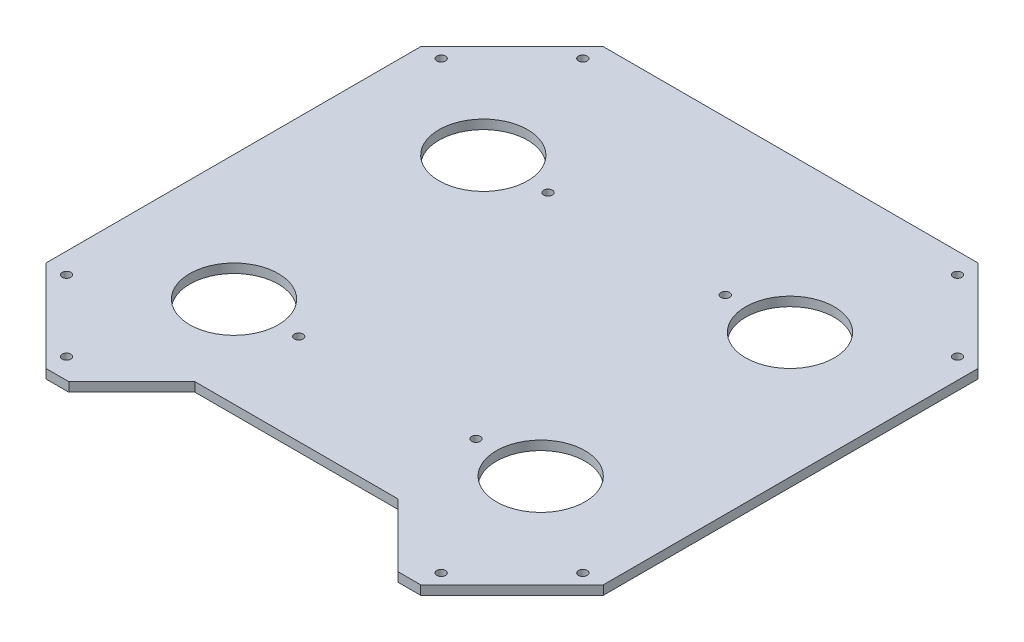
SolidWorks part; units mm, degrees
ref_plane "Front Plane" through (0, 0, 0) normal (0, 0, 1) x (1, 0, 0)
ref_plane "Top Plane" through (0, 0, 0) normal (0, 1, 0) x (1, 0, 0)
ref_plane "Right Plane" through (0, 0, 0) normal (1, 0, 0) x (0, 0, -1)
sketch "Sketch1" plane through (0, 0, 0) normal (0, 1, 0) x (1, 0, 0)
  line L0 (0, 0) -> (0, 724.3659) construction
  line L1 (0, 0) -> (205, 0)
  line L2 (305, 100) -> (305, 510)
  line L3 (205, 610) -> (-205, 610)
  line L4 (-305, 510) -> (-305, 100)
  line L6 (-305, 510) -> (-205, 610)
  line L7 (-205, 0) -> (205, 0)
  line L10 (0, 0) -> (205, 0)
  line L11 (305, 510) -> (205, 610)
  line L12 (305, 305) -> (-562.9514, 305) construction
  line L14 (-305, 100) -> (-205, 0)
  line L15 (305, 100) -> (205, 0)
  line L16 (-205, 610) -> (-305, 510)
  line L17 (-205, 610) -> (-136.4106, 541.4106)
  line L18 (-305, 510) -> (-236.4106, 441.4106)
  line L19 (-136.4106, 541.4106) -> (-236.4106, 441.4106)
  line L20 (305, 510) -> (205, 610)
  line L21 (305, 510) -> (236.4106, 441.4106)
  line L22 (136.4106, 541.4106) -> (236.4106, 441.4106)
  line L23 (205, 610) -> (136.4106, 541.4106)
  line L24 (305, 100) -> (236.4106, 168.5894)
  line L25 (305, 100) -> (205, 0)
  line L26 (136.4106, 68.5894) -> (236.4106, 168.5894)
  line L27 (205, 0) -> (136.4106, 68.5894)
  line L28 (-305, 100) -> (-205, 0)
  line L29 (-305, 100) -> (-236.4106, 168.5894)
  line L30 (-205, 0) -> (-136.4106, 68.5894)
  line L31 (-136.4106, 68.5894) -> (-236.4106, 168.5894)
  line L32 (205, 610) -> (136.4106, 541.4106)
  line L33 (205, 610) -> (305, 510)
  line L34 (136.4106, 541.4106) -> (236.4106, 441.4106)
  line L35 (305, 510) -> (236.4106, 441.4106)
  line L36 (-305, 100) -> (-205, 0)
  line L37 (-305, 100) -> (-236.4106, 168.5894)
  line L38 (-205, 0) -> (-136.4106, 68.5894)
  line L39 (-236.4106, 168.5894) -> (-136.4106, 68.5894)
  line L40 (236.4106, 168.5894) -> (136.4106, 68.5894)
  line L41 (236.4106, 168.5894) -> (305, 100)
  line L42 (136.4106, 68.5894) -> (205, 0)
  line L43 (305, 100) -> (205, 0)
  line L45 (0, 610) -> (-84.25, 610)
  line L46 (0, 0) -> (-84.25, 0)
  line L47 (-84.25, 610) -> (-84.25, 0)
  line L48 (84.25, 610) -> (84.25, 0)
  line L49 (-84.25, 610) -> (84.25, 610)
  line L50 (-84.25, 610) -> (-84.25, 0)
  line L51 (84.25, 610) -> (84.25, 0)
  line L52 (-84.25, 0) -> (84.25, 0)
  line L53 (-167.8213, 441.4106) -> (-97, 441.4106)
  line L54 (-84.25, 76.4) -> (84.25, 76.4)
  line L55 (-84.25, 76.4) -> (-84.25, 533.6)
  line L56 (84.25, 76.4) -> (84.25, 533.6)
  line L57 (-84.25, 533.6) -> (84.25, 533.6)
  line L70 (-305, 510) -> (-236.4106, 441.4106)
  circle A0 centre (-167.8213, 441.4106) radius 48.5
  circle A1 centre (-167.8213, 168.5894) radius 48.5
  circle A2 centre (167.8213, 168.5894) radius 48.5
  circle A3 centre (167.8213, 441.4106) radius 48.5
  arc A4 (-84.25, 76.4) -> (84.25, 76.4) centre (0, 76.4) ccw
  circle A9 centre (-97, 441.4106) radius 4.7625
  circle A10 centre (97, 441.4106) radius 4.7625
  circle A11 centre (97, 168.5894) radius 4.7625
  circle A12 centre (-97, 168.5894) radius 4.7625
  point P47 (-270.7053, 475.7053)
  dimension "D6" = 97
  dimension "D10" = 48.5
  dimension "D15" = 9.525
  dimension "D16" = 48.5
  dimension "D1" = 610
  dimension "D2" = 610
  dimension "D3" = 97
  dimension "D4" = 45
  dimension "D5" = 100
  dimension "D7" = 168.5
  dimension "D8" = 84.25
  dimension "D9" = 84.25
  dimension "D11" = 457.2
  dimension "D13" = 533.6
  dimension "D14" = 194
extrude "Boss-Extrude1" add sketch "Sketch1" along normal blind 10 contours L19 L17 L6 L18 | L39 A1 L31 L30 L7 L47 L3 L17 L19 A0 L18 L4 L29 | L30 L31 L39 L29 L14 | L48 L3 L47 L7 L1 | L34 A3 L22 L23 L3 L48 L10 L27 L26 A2 L40 L24 L2 L21 | L11 L23 L22 L34 L21 | L27 L15 L24 L40 L26 | L54 L55 L57 L56 | L49 L50 L52 L51
sketch "Sketch2" plane through (0, 10, 0) normal (0, 1, 0) x (1, 0, 0)
  line L4 (-205, 0) -> (-180, 0)
  line L5 (-180, 0) -> (-111, 69)
  line L6 (-180, 0) -> (180, 0)
  line L7 (180, 0) -> (111, 69)
  line L8 (111, 69) -> (-111, 69)
  line L10 (180, 0) -> (205, 0)
  line M5 (-205, 0) -> (205, 0)
  dimension "D1" = 25
  dimension "D2" = 25
  dimension "D3" = 45
  dimension "D4" = 69
  dimension "D5" = 45
extrude "Cut-Extrude1" cut sketch "Sketch2" against normal blind 5000 contours L7 L8 L5 M5
sketch "Sketch3" plane through (0, 10, 0) normal (0, 1, 0) x (1, 0, 0)
  line L0 (0, 0) -> (0, 610) construction
  line L1 (-305, 305) -> (305, 305) construction
  line L2 (-305, 100) -> (-205, 0) construction
  line L4 (-282.5423, 100) -> (-293.7711, 88.7711)
  line L5 (205, 610) -> (-205, 610) construction
  line L6 (-305, 510) -> (-305, 100) construction
  line L7 (305, 100) -> (305, 510) construction
  line L8 (-180, 0) -> (-111, 69) construction
  circle A0 centre (-205, 22.4577) radius 4.7625
  circle A1 centre (205, 22.4577) radius 4.7625
  circle A2 centre (-282.5423, 100) radius 4.7625
  circle A3 centre (282.5423, 100) radius 4.7625
  circle A4 centre (282.5423, 510) radius 4.7625
  circle A5 centre (205, 587.5423) radius 4.7625
  circle A6 centre (-205, 587.5423) radius 4.7625
  circle A7 centre (-282.5423, 510) radius 4.7625
  dimension "D1" = 9.525
  dimension "D2" = 9.525
  dimension "D6" = 15.88
  dimension "D5" = 33.5577
  dimension "D3" = 15.88
  dimension "D4" = 15.88
  dimension "D7" = 15.88
extrude "Cut-Extrude2" cut sketch "Sketch3" against normal blind 5000 contours A2 | A0 | A1 | A3 | A4 | A5 | A6 | A7
